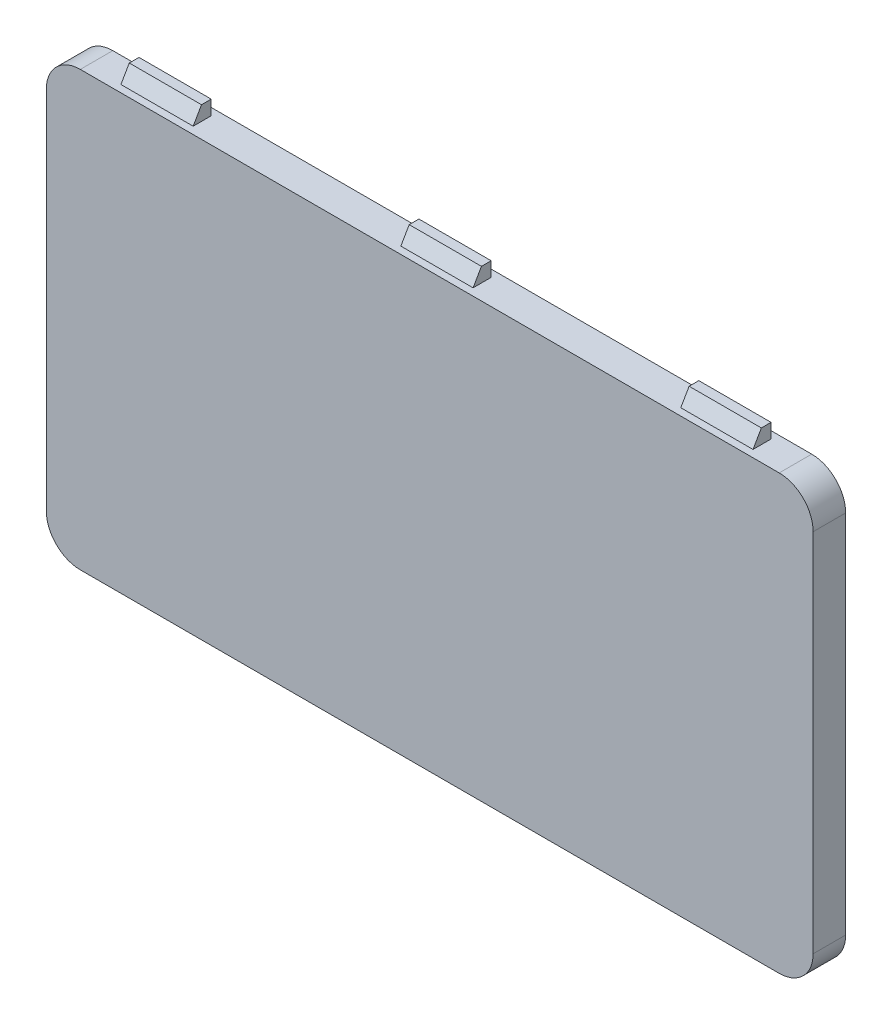
SolidWorks part; units mm, degrees
material "ABS"
ref_plane "Front Plane" through (0, 0, 0) normal (0, 0, 1) x (1, 0, 0)
ref_plane "Top Plane" through (0, 0, 0) normal (0, 1, 0) x (1, 0, 0)
ref_plane "Right Plane" through (0, 0, 0) normal (1, 0, 0) x (0, 0, -1)
sketch "Sketch1" plane through (0, 0, 0) normal (0, 0, 1) x (1, 0, 0)
  line L37 (-21.23, 10.12) -> (-21.23, -10.12)
  line L38 (-19.35, -12) -> (19.35, -12)
  line L39 (21.23, -10.12) -> (21.23, 10.12)
  line L40 (19.35, 12) -> (-19.35, 12)
  line L41 (-21.23, 10.12) -> (-21.23, -10.12)
  line L42 (-19.35, -12) -> (19.35, -12)
  line L43 (21.23, -10.12) -> (21.23, 10.12)
  line L44 (19.35, 12) -> (-19.35, 12)
  arc A39 (-21.23, -10.12) -> (-19.35, -12) centre (-19.35, -10.12) ccw
  arc A40 (19.35, -12) -> (21.23, -10.12) centre (19.35, -10.12) ccw
  arc A41 (21.23, 10.12) -> (19.35, 12) centre (19.35, 10.12) ccw
  arc A42 (-19.35, 12) -> (-21.23, 10.12) centre (-19.35, 10.12) ccw
  arc A43 (-21.23, -10.12) -> (-19.35, -12) centre (-19.35, -10.12) ccw
  arc A44 (19.35, -12) -> (21.23, -10.12) centre (19.35, -10.12) ccw
  arc A45 (21.23, 10.12) -> (19.35, 12) centre (19.35, 10.12) ccw
  arc A46 (-19.35, 12) -> (-21.23, 10.12) centre (-19.35, 10.12) ccw
  dimension "D1" = 0.2
extrude "Boss-Extrude1" add sketch "Sketch1" along normal blind 1.8
sketch "Sketch4" plane through (0, 0, 0) normal (1, 0, 0) x (0, 0, -1)
  line L0 (-1.4, 12) -> (-0.9381, 12.8)
  line L2 (-0.9381, 12.8) -> (-0.4, 12.8)
  line L3 (-0.4, 12.8) -> (-0.4, 12)
  line L4 (-0.4, 12) -> (-1.4, 12)
  line L7 (-1.8, 12) -> (-1.8, 10.12) construction
  line L8 (-1.8, 12) -> (0, 12) construction
  dimension "D1" = 0.8
  dimension "D2" = 0.5381
  dimension "D3" = 0.4
  dimension "D4" = 1
  dimension "D5" = 60
extrude "Latch" add sketch "Sketch4" along normal mid plane 4
mirror "Mirror1" about plane through (0, 0, 0) normal (0, 1, 0) of "Latch"
pattern_linear "LPattern1" count 2 spacing 15.5 along (1, 0, 0) of "Mirror1", "Latch"
pattern_linear "LPattern2" count 2 spacing 15.5 along (-1, 0, 0) of "Mirror1", "Latch"
